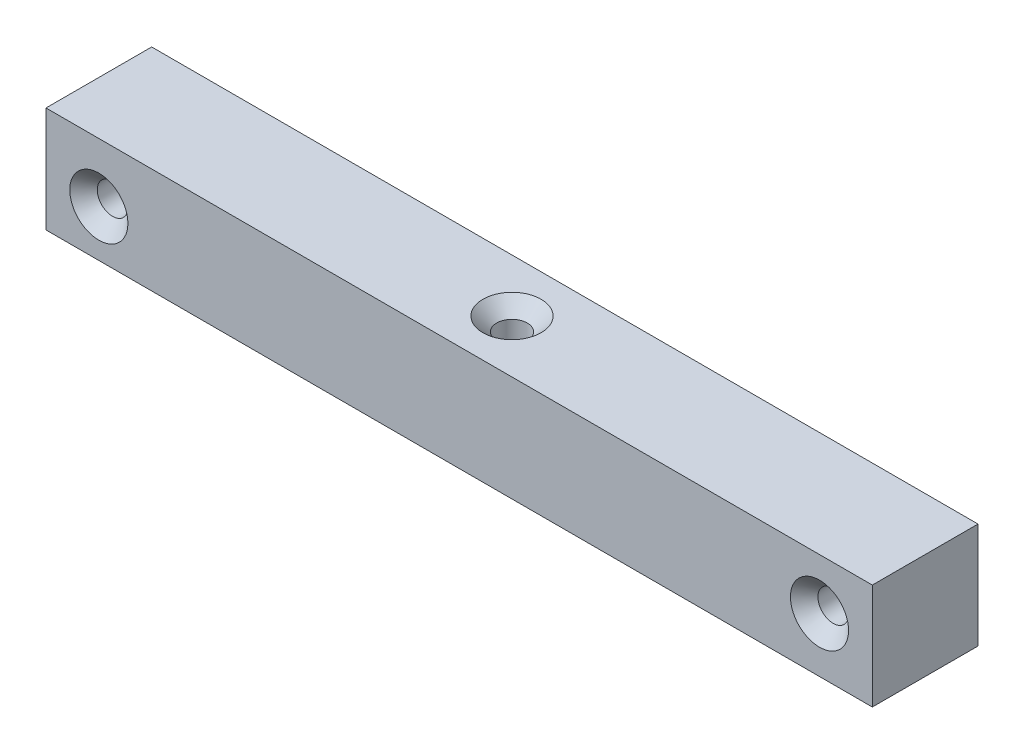
SolidWorks part; units mm, degrees
ref_plane "Front Plane" through (0, 0, 0) normal (0, 0, 1) x (1, 0, 0)
ref_plane "Top Plane" through (0, 0, 0) normal (0, 1, 0) x (1, 0, 0)
ref_plane "Right Plane" through (0, 0, 0) normal (1, 0, 0) x (0, 0, -1)
sketch "Sketch1" plane through (0, 0, 0) normal (0, 1, 0) x (1, 0, 0)
  line L1 (0, 0) -> (-78.2, 0)
  line L2 (0, 0) -> (0, -10)
  line L3 (0, -10) -> (-78.2, -10)
  line L4 (-78.2, 0) -> (-78.2, -10)
  dimension "D1" = 78.2
  dimension "D2" = 10
extrude "Boss-Extrude1" add sketch "Sketch1" along normal blind 10
hole_wizard "CSK for M2.5 Flat Head Machine Screw1" positions "Sketch6" profile "Sketch7" countersink size "M2.5" standard "ANSI Metric" end condition through all
sketch "Sketch6" plane through (0, 0, 10) normal (0, 0, 1) x (1, 0, 0)
  line L0 (0, 10) -> (0, 0) construction
  point P0 (-5, 5.1542)
  point P5 (0, 5)
  dimension "D1" = 5
sketch "Sketch7" plane through (-5, 5.1542, 10) normal (1, 0, 0) x (0, -1, 0)
  line L0 (0, 0) -> (0, 10)
  line L1 (0, 10) -> (1.45, 10)
  line L2 (1.45, 10) -> (1.45, 1.3)
  line L3 (1.45, 1.3) -> (2.75, 0)
  line L5 (2.75, 0) -> (0, 0)
  line L6 (-1.45, 1.3) -> (-2.75, 0) construction
  line L11 (0, -6.35) -> (0, 107.95) construction
  dimension "Thru Hole Dia." = 2.9
  dimension "Thru Hole Depth" = 10
  dimension "Near C'Sink Dia." = 5.5
  dimension "Near C'Sink Angle" = 90
hole_wizard "CSK for M2.5 Flat Head Machine Screw2" positions "Sketch10" profile "Sketch11" countersink size "M2.5" standard "ANSI Metric" end condition through all
sketch "Sketch10" plane through (0, 0, 10) normal (0, 0, 1) x (1, 0, 0)
  circle A0 centre (-5, 5.1542) radius 1.45 construction
  point P0 (-73.199, 4.4145)
  point P5 (0, 0)
  point P8 (0, 0)
  point P9 (0, 0)
  dimension "D1" = 68.199
sketch "Sketch11" plane through (-73.199, 4.4145, 10) normal (1, 0, 0) x (0, -1, 0)
  line L0 (0, 0) -> (0, 10)
  line L1 (0, 10) -> (1.45, 10)
  line L2 (1.45, 10) -> (1.45, 1.3)
  line L3 (1.45, 1.3) -> (2.75, 0)
  line L5 (2.75, 0) -> (0, 0)
  line L6 (-1.45, 1.3) -> (-2.75, 0) construction
  line L11 (0, -6.35) -> (0, 107.95) construction
  dimension "Thru Hole Dia." = 2.9
  dimension "Thru Hole Depth" = 10
  dimension "Near C'Sink Dia." = 5.5
  dimension "Near C'Sink Angle" = 90
hole_wizard "CSK for M2.5 Flat Head Machine Screw3" positions "Sketch12" profile "Sketch13" countersink size "M2.5" standard "ANSI Metric" end condition through all
sketch "Sketch12" plane through (0, 10, 0) normal (0, 1, 0) x (1, 0, 0)
  line L0 (0, -10) -> (0, 0) construction
  line L1 (0, 0) -> (-78.2, 0) construction
  point P0 (-39.1, -5)
  point P5 (0, -5)
  point P6 (0, 0)
  dimension "D1" = 39.1
  dimension "D2" = 5
sketch "Sketch13" plane through (-39.1, 10, 5) normal (1, 0, 0) x (0, 0, 1)
  line L0 (0, 0) -> (0, 10)
  line L1 (0, 10) -> (1.45, 10)
  line L2 (1.45, 10) -> (1.45, 1.3)
  line L3 (1.45, 1.3) -> (2.75, 0)
  line L5 (2.75, 0) -> (0, 0)
  line L6 (-1.45, 1.3) -> (-2.75, 0) construction
  line L11 (0, -6.35) -> (0, 107.95) construction
  dimension "Thru Hole Dia." = 2.9
  dimension "Thru Hole Depth" = 10
  dimension "Near C'Sink Dia." = 5.5
  dimension "Near C'Sink Angle" = 90
